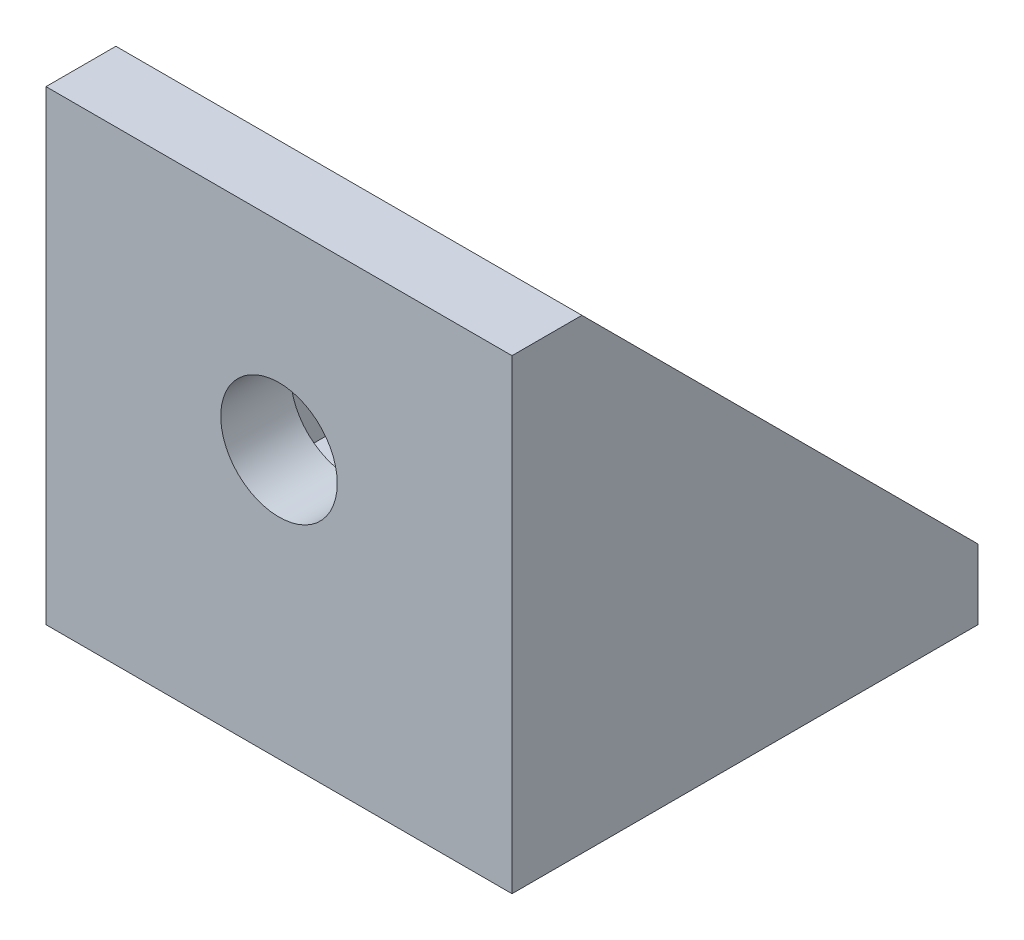
SolidWorks part; units mm, degrees
material "Aleación 1060"
ref_plane "Alzado" through (0, 0, 0) normal (0, 0, 1) x (1, 0, 0)
ref_plane "Planta" through (0, 0, 0) normal (0, 1, 0) x (1, 0, 0)
ref_plane "Vista lateral" through (0, 0, 0) normal (1, 0, 0) x (0, 0, -1)
sketch "Croquis1" plane through (0, 0, 0) normal (0, 1, 0) x (1, 0, 0)
  line L1 (-10, 10) -> (10, 10)
  line L2 (-10, 10) -> (-10, -10)
  line L3 (-10, -10) -> (10, -10)
  line L4 (10, 10) -> (10, -10)
  line L5 (-10, 10) -> (10, -10) construction
  line L6 (-10, -10) -> (10, 10) construction
  point P0 (0, 0)
  dimension "D1" = 20
extrude "Saliente-Extruir1" add sketch "Croquis1" along normal blind 3
sketch "Croquis3" plane through (0, 0, 0) normal (0, 0, 1) x (1, 0, 0)
  line L1 (-10, 20) -> (10, 20)
  line L2 (-10, 20) -> (-10, 0)
  line L3 (-10, 0) -> (10, 0)
  line L4 (10, 20) -> (10, 0)
  line L5 (-10, 20) -> (10, 0) construction
  line L6 (-10, 0) -> (10, 20) construction
  point P0 (0, 10)
  dimension "D1" = 20
extrude "Saliente-Extruir2" add sketch "Croquis3" against normal blind 3 from surface at 10 starting at face at (0, 1.5, 10)
sketch "Croquis4" plane through (0, 0, 0) normal (1, 0, 0) x (0, 0, -1)
  line L0 (-7, 20) -> (10, 3)
  line L1 (-7, 20) -> (-7, 3)
  line L2 (-7, 3) -> (10, 3)
extrude "Saliente-Extruir3" add sketch "Croquis4" against normal blind 2 from surface at 10 starting at face at (10, 7.6667, 2.3333)
sketch "Croquis8" plane through (0, 0, 0) normal (1, 0, 0) x (0, 0, -1)
  line L3 (10, 3) -> (-7, 20)
  line L4 (-7, 3) -> (10, 3)
  line L5 (-7, 20) -> (-7, 3)
  line L6 (10, 3) -> (-7, 20)
  line L7 (-7, 3) -> (10, 3)
  line L8 (-7, 20) -> (-7, 3)
  dimension "D1" = 0
extrude "Saliente-Extruir4" add sketch "Croquis8" along normal blind 2 from surface at -10 starting at face at (-10, 7.6667, 2.3333)
sketch "Croquis6" plane through (0, 0, 0) normal (0, 1, 0) x (1, 0, 0)
  line L0 (-8, 10) -> (8, -7) construction
  circle A1 centre (0, 1.5) radius 2.5
  dimension "D1" = 5
extrude "Cortar-Extruir3" cut sketch "Croquis6" against normal through all and the other way through all
sketch "Croquis7" plane through (0, 0, 0) normal (0, 0, 1) x (1, 0, 0)
  line L0 (8, 20) -> (-8, 3) construction
  circle A0 centre (0, 11.5) radius 2.5
  dimension "D1" = 5
extrude "Cortar-Extruir4" cut sketch "Croquis7" against normal through all both and the other way through all
